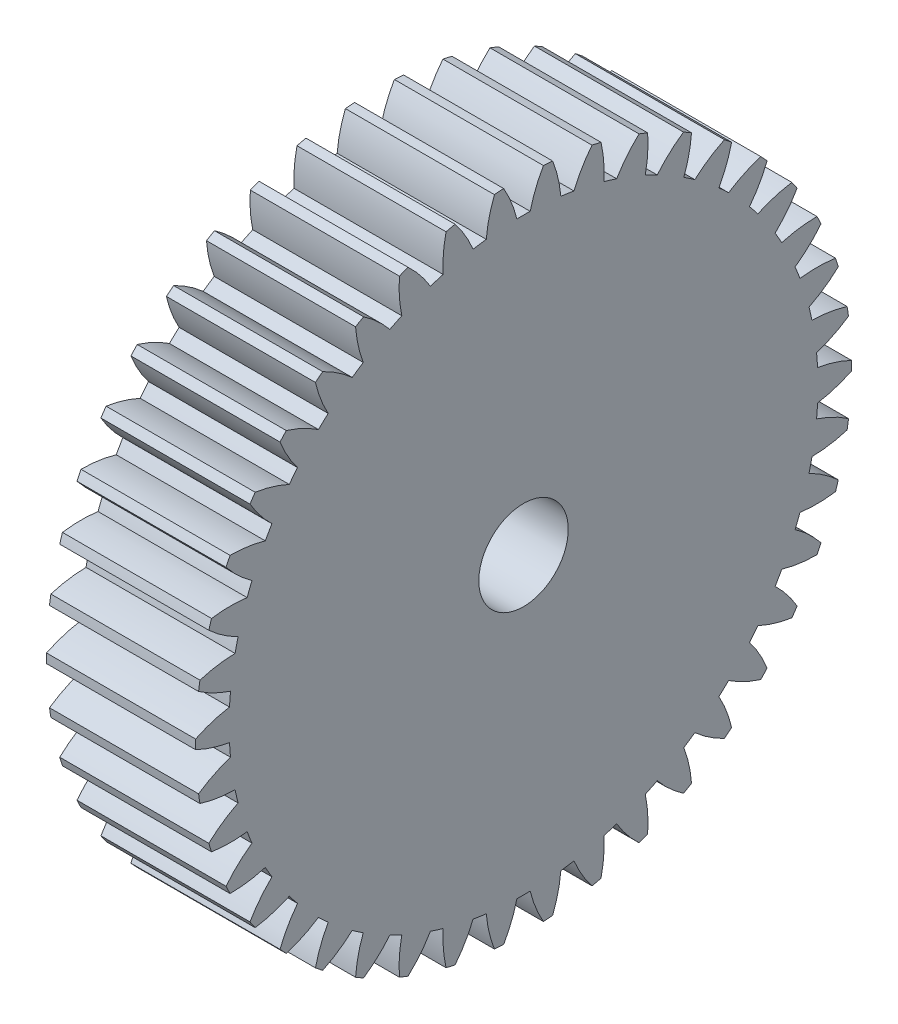
SolidWorks part; units mm, degrees
ref_plane "Plane1" through (0, 0, 0) normal (0, 0, 1) x (1, 0, 0)
ref_plane "Plane2" through (0, 0, 0) normal (0, 1, 0) x (1, 0, 0)
ref_plane "Plane3" through (0, 0, 0) normal (1, 0, 0) x (0, 0, -1)
other "Configuration Table"
sketch "HoldingSke" plane through (0, 0, 0) normal (0, 1, 0) x (1, 0, 0)
  line L0 (0, 0) -> (0.7431, -0.6691)
  line L1 (-15, 0) -> (100, 0) construction
  line L2 (0, 0) -> (-2.1039, 2.3779)
  line L3 (0, 0) -> (-11.863, 4.5341)
  line L4 (0, 0) -> (6.4178, 5.7786)
  line L5 (0, 0) -> (-46.8476, -17.4728)
  line L6 (0, 0) -> (-8.2896, -5.593)
  line L7 (-2.1039, 2.3779) -> (8.6586, 51.2059)
  line L8 (-76.2, 54.61) -> (-75.2, 54.61)
  line L9 (-71.009, 38.7566) -> (-53.1078, 45.2721)
  line L10 (-76.2, 71.12) -> (104.1128, 71.12)
  line L11 (0, 0) -> (-10, 0)
  line L12 (-76.2, 101.6) -> (-76.162, 101.6)
  line L13 (24.9733, 27.94) -> (52.9518, 28.4284)
  line L14 (24.9733, 27.94) -> (24.9743, 27.94)
  line L15 (24.9733, 27.94) -> (100.4006, 29.5858)
  line L16 (-63.627, -1) -> (-12.827, -1)
  circle A0 centre (0, 0) radius 3
  circle A1 centre (0, 0) radius 19.749
  circle A2 centre (0, 0) radius 37.5
  circle A3 centre (0, 0) radius 3
  dimension "MHD" = 39.498
  dimension "Hub_dia" = 75
  dimension "Bore" = 6
  dimension "MBD" = 6
  dimension "Num_teeth" = 42
  dimension "Pitch" = 1
  dimension "Overall_len" = 50
  dimension "Show_teeth" = 42
  dimension "Thickness" = 10
  dimension "OAL" = 50.0001
  dimension "T_dim" = 1
  dimension "Ap" = 20
  dimension "H" = 19.05
  dimension "Pitch_radius" = 180.3128
  dimension "Width" = 10
  dimension "Backlash" = 0.038
  dimension "Addendum_fac" = 1
  dimension "Dedendum_fac" = 1.25
  dimension "Clearance_fac" = 0.25
  dimension "Dedendum_add" = 0.001
  dimension "Module" = 1
sketch "BasProSke" plane through (0, 0, 0) normal (0, 1, 0) x (1, 0, 0)
  line L0 (-10, 0) -> (60, 0) construction
  line L1 (0, 0) -> (0, 22)
  line L2 (0, 0) -> (10, 0)
  line L3 (10, 0) -> (10, 22)
  line L4 (10, 22) -> (0, 22)
  dimension "Thickness" = 10
  dimension "Diameter" = 44
revolve "Base-Revolve" add sketch "BasProSke" angle 360 about L0
sketch "TooCutSke" plane through (0, 0, 0) normal (1, 0, 0) x (0, 0, -1)
  line L1 (0, 0) -> (0, 107) construction
  line L2 (0, 0) -> (-0.8517, 20.9827) construction
  line L3 (0, 0) -> (-3.1368, 41.858) construction
  line L4 (-0.8517, 20.9827) -> (-1.5684, 20.929) construction
  arc A0 (0.4461, 19.744) -> (-0.4461, 19.744) centre (0, 0) ccw
  arc A1 (1.3487, 21.9841) -> (-1.3487, 21.9841) centre (0, 0) ccw
  circle A2 centre (0, 0) radius 21 construction
  circle A3 centre (0, 0) radius 19.7335 construction
  arc A4 (-0.4461, 19.744) -> (-1.3487, 21.9841) centre (-8.6078, 17.7572) ccw
  arc A5 (1.3487, 21.9841) -> (0.4461, 19.744) centre (8.6078, 17.7572) ccw
  dimension "Root_dia" = 39.498
  dimension "Overcut_dia" = 44.0508
  dimension "Pitch_dia" = 42
  dimension "Base_dia" = 39.4671
  dimension "Flank_rad" = 8.4
  dimension "Half_ang" = 4.286
  dimension "Half_CT" = 0.7187
extrude "ToothCut" cut sketch "TooCutSke" along normal through all
fillet "Breaks" [suppressed] radius 0.02
fillet "RootFillets" [suppressed] radius 0.251
pattern_circular "TeethCuts" count 42 every 8.571 about axis through (-10, 0, 0) along (1, 0, 0) of "ToothCut", "RootFillets", "Breaks"
sketch "HubNeaOneSke" plane through (0, 0, 0) normal (-1, 0, 0) x (0, 0, 1)
  circle A0 centre (0, 0) radius 19.749
  dimension "Diameter" = 39.498
extrude "HubNearOne" [suppressed] add sketch "HubNeaOneSke" along normal blind 40.0001
sketch "HubNeaBotSke" plane through (0, 0, 0) normal (-1, 0, 0) x (0, 0, 1)
  circle A0 centre (0, 0) radius 19.749
  dimension "Diameter" = 39.498
extrude "HubNearBoth" [suppressed] add sketch "HubNeaBotSke" along normal blind 20
ref_plane "FarPln" through (10, 0, 0) normal (1, 0, 0) x (0, 0, -1)
sketch "HubFarSke" plane through (10, 0, 0) normal (1, 0, 0) x (0, 0, -1)
  circle A0 centre (0, 0) radius 19.749
  dimension "Diameter" = 39.498
extrude "HubFar" [suppressed] add sketch "HubFarSke" along normal blind 20
sketch "BorSke" plane through (0, 0, 0) normal (1, 0, 0) x (0, 0, -1)
  circle A0 centre (0, 0) radius 3
  dimension "Diameter" = 6
extrude "Bore" cut sketch "BorSke" along normal mid plane 100.0001
sketch "KeySke" plane through (0, 0, 0) normal (1, 0, 0) x (0, 0, -1)
  line L0 (-1, 0) -> (-1, 4)
  line L1 (-1, 4) -> (1, 4)
  line L2 (1, 4) -> (1, 0)
  line L3 (0, 0) -> (0, 34) construction
  line L4 (-1, 0) -> (1, 0)
  dimension "Offset" = 4
  dimension "Width" = 2
extrude "Keyway" [suppressed] cut sketch "KeySke" along normal mid plane 100.0001
pattern_circular "Keyway2" [suppressed] count 2 every 90 about axis through (-10, 0, 0) along (1, 0, 0)
equation "' \"Module@HoldingSke\" = 6.35"
equation "' \"Num_teeth@HoldingSke\" = 12"
equation "' \"Ap@HoldingSke\" =  20"
equation "' \"Ap@HoldingSke\" = 20"
equation "' \"Width@HoldingSke\" = 0.5 * 25.4"
equation "' \"Hub_dia@HoldingSke\"= 1 * 25.4"
equation "' \"Hub_dia@HoldingSke\" = 1 * 25.4"
equation "' \"Overall_len@HoldingSke\" = 1.0 * 25.4"
equation "' \"Bore@HoldingSke\" = 0.75 * 25.4"
equation "' \"T_dim@HoldingSke\" = 0.1 * 25.4"
equation "' \"Width@KeySke\" = 0.25 * 25.4"
equation "' \"Show_teeth@HoldingSke\" = 13"
equation "' \"Backlash@HoldingSke\" = 0.009 * 25.4"
equation "' \"Addendum_fac@HoldingSke\" = 1.0"
equation "' \"Dedendum_fac@HoldingSke\" = 1.25"
equation "' \"Dedendum_add@HoldingSke\" = 0.00005 * 25.4"
equation "' \"Clearance_fac@HoldingSke\" = 0.25"
equation "\"Pitch@HoldingSke\" = 1 / \"Module@HoldingSke\""
equation "\"Overcut_dia@TooCutSke\" = (\"Num_teeth@HoldingSke\" + 2 * \"Addendum_fac@HoldingSke\") / \"Pitch@HoldingSke\" + 0.002 * 25.4"
equation "\"Pitch_dia@TooCutSke\" = \"Num_teeth@HoldingSke\" / \"Pitch@HoldingSke\""
equation "\"Base_dia@TooCutSke\" = \"Num_teeth@HoldingSke\" / \"Pitch@HoldingSke\" * cos((\"Ap@HoldingSke\"  * 3.14159265 / 180))"
equation "\"Root_dia@TooCutSke\" = (\"Num_teeth@HoldingSke\" + 2) / \"Pitch@HoldingSke\" - 2 * (\"Addendum_fac@HoldingSke\" + \"Dedendum_fac@HoldingSke\") / \"Pitch@HoldingSke\" - \"Dedendum_add@HoldingSke\" * 2"
equation "\"Half_ang@TooCutSke\" = 180 / \"Num_teeth@HoldingSke\""
equation "\"Half_CT@TooCutSke\" = \"Num_teeth@HoldingSke\" / \"Pitch@HoldingSke\" * sin((3.14159265 / 2 / \"Num_teeth@HoldingSke\")) / 2 - 7 * \"Backlash@HoldingSke\" / 4"
equation "\"Flank_rad@TooCutSke\" = \"Num_teeth@HoldingSke\" / \"Pitch@HoldingSke\" / 5"
equation "\"Radius@RootFillets\" = \"Clearance_fac@HoldingSke\" / \"Pitch@HoldingSke\" + \"Dedendum_add@HoldingSke\""
equation "\"Break_rad@Breaks\" = 0.02 / \"Pitch@HoldingSke\""
equation "\"Thickness@HoldingSke\" = \"Width@HoldingSke\""
equation "\"OAL@HoldingSke\" = \"Thickness@HoldingSke\""
equation "\"MHD@HoldingSke\" = (\"Num_teeth@HoldingSke\" + 2) / \"Pitch@HoldingSke\" - 2 * (\"Addendum_fac@HoldingSke\" + \"Dedendum_fac@HoldingSke\")  / \"Pitch@HoldingSke\" - \"Dedendum_add@HoldingSke\" * 2"
equation "\"MBD@HoldingSke\" = (\"Num_teeth@HoldingSke\" + 2) / \"Pitch@HoldingSke\" - 2 * (\"Addendum_fac@HoldingSke\" + \"Dedendum_fac@HoldingSke\")  / \"Pitch@HoldingSke\" - \"Dedendum_add@HoldingSke\" * 2 - 0.002 * 25.4"
equation "\"MHD@HoldingSke\" = ((sgn( \"MHD@HoldingSke\" - \"Hub_dia@HoldingSke\" )-1)*( \"MHD@HoldingSke\" - \"Hub_dia@HoldingSke\" ))/-2+ \"Hub_dia@HoldingSke\""
equation "\"MBD@HoldingSke\" = ((sgn( \"MBD@HoldingSke\" - \"Bore@HoldingSke\" )-1)*( \"MBD@HoldingSke\" - \"Bore@HoldingSke\" ))/-2+ \"Bore@HoldingSke\""
equation "\"OAL@HoldingSke\" = ((sgn( \"OAL@HoldingSke\" - \"Overall_len@HoldingSke\" )+1)*( \"OAL@HoldingSke\" - \"Overall_len@HoldingSke\" ))/2 + \"Overall_len@HoldingSke\" + 0.000002 * 25.4"
equation "\"Num_teeth@TeethCuts\" = int( \"Show_teeth@HoldingSke\" ) + 1"
equation "\"Num_teeth@TeethCuts\" = ((sgn( \"Num_teeth@TeethCuts\" - \"Num_teeth@HoldingSke\" )-1)*( \"Num_teeth@TeethCuts\" - \"Num_teeth@HoldingSke\" ))/-2+ \"Num_teeth@HoldingSke\""
equation "\"Num_teeth@TeethCuts\" = ((sgn( \"Num_teeth@TeethCuts\" - 2.0)+1)*( \"Num_teeth@TeethCuts\" - 2.0))/2 +2.0"
equation "\"Angle@TeethCuts\" = 360.0 / \"Num_teeth@HoldingSke\""
equation "\"Diameter@BasProSke\" = (\"Num_teeth@HoldingSke\" + 2 * \"Addendum_fac@HoldingSke\") / \"Pitch@HoldingSke\""
equation "\"Thickness@BasProSke\"  = \"Thickness@HoldingSke\""
equation "' \"Fillet_rad@BasProSke\" =  \"Thickness@HoldingSke\" * 0.05"
equation "' \"Fillet_rad@BasProSke\" = \"Thickness@HoldingSke\" * 0.05"
equation "\"MHD@HoldingSke\" = ((sgn( \"MHD@HoldingSke\" - \"Root_dia@TooCutSke\" )-1)*( \"MHD@HoldingSke\" - \"Root_dia@TooCutSke\" ))/-2+ \"Root_dia@TooCutSke\""
equation "\"Diameter@HubNeaOneSke\" = \"MHD@HoldingSke\""
equation "\"Length@HubNearOne\" = \"OAL@HoldingSke\" - \"Thickness@BasProSke\""
equation "\"Diameter@HubNeaBotSke\" = \"MHD@HoldingSke\""
equation "\"Length@HubNearBoth\" = ( \"OAL@HoldingSke\" - \"Thickness@BasProSke\" ) / 2.0"
equation "\"Thickness@FarPln\" = \"Thickness@BasProSke\""
equation "\"Diameter@HubFarSke\" = \"MHD@HoldingSke\""
equation "\"Length@HubFar\" = ( \"OAL@HoldingSke\" - \"Thickness@BasProSke\" ) / 2.0"
equation "\"Diameter@BorSke\" = \"MBD@HoldingSke\""
equation "\"D1@Bore\" = \"OAL@HoldingSke\" * 2.0"
equation "\"D1@Keyway\" = \"OAL@HoldingSke\" * 2.0"
equation "\"Offset@KeySke\" = \"T_dim@HoldingSke\" + \"MBD@HoldingSke\" / 2.0"
